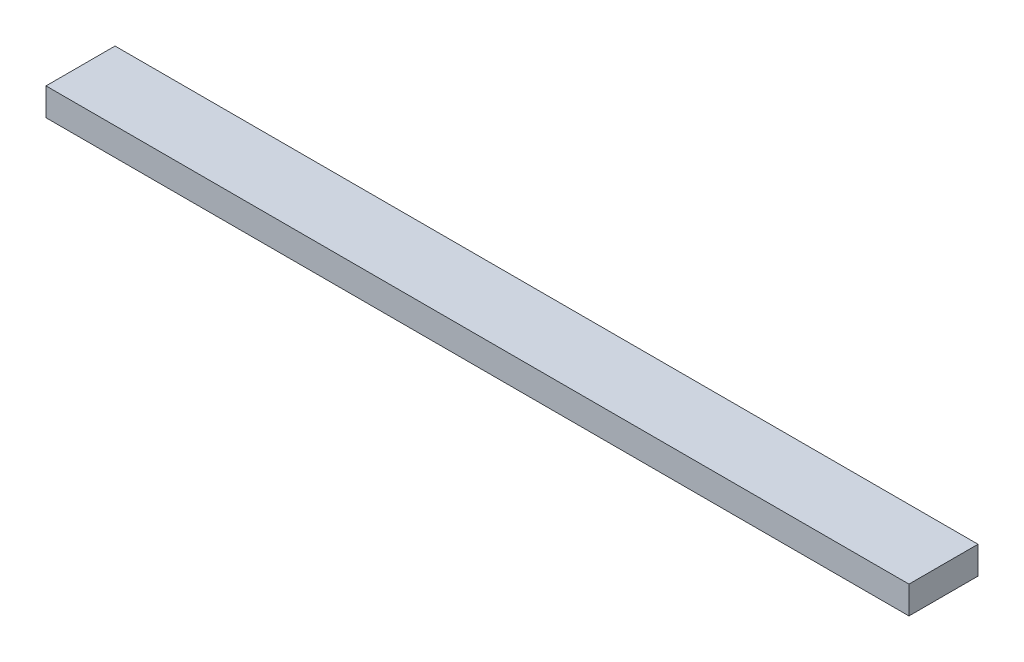
SolidWorks part; units mm, degrees
ref_plane "Спереди" through (0, 0, 0) normal (0, 0, 1) x (1, 0, 0)
ref_plane "Сверху" through (0, 0, 0) normal (0, 1, 0) x (1, 0, 0)
ref_plane "Справа" through (0, 0, 0) normal (1, 0, 0) x (0, 0, -1)
other "Configuration Table"
sketch "Эскиз1" plane through (0, 0, 0) normal (0, 1, 0) x (1, 0, 0)
  line L1 (25, -2) -> (-25, -2)
  line L2 (25, -2) -> (25, 2)
  line L3 (25, 2) -> (-25, 2)
  line L4 (-25, -2) -> (-25, 2)
  line L5 (0, 2) -> (0, -2) construction
  line L6 (25, 0) -> (-25, 0) construction
  point P0 (0, 0)
  dimension "D1" = 2
  dimension "D2" = 50
extrude "Бобышка-Вытянуть1" add sketch "Эскиз1" along normal blind 1.6
